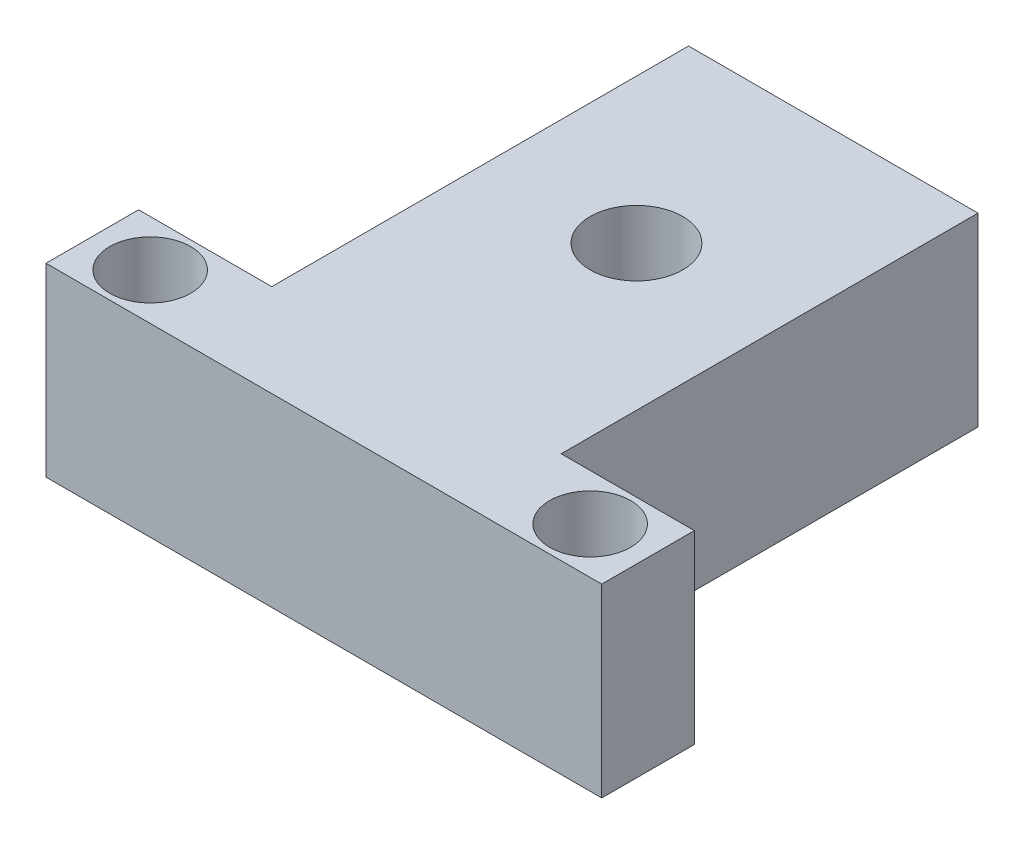
SolidWorks part; units mm, degrees
ref_plane "Front Plane" through (0, 0, 0) normal (0, 0, 1) x (1, 0, 0)
ref_plane "Top Plane" through (0, 0, 0) normal (0, 1, 0) x (1, 0, 0)
ref_plane "Right Plane" through (0, 0, 0) normal (1, 0, 0) x (0, 0, -1)
sketch "Sketch1" plane through (0, 0, 0) normal (0, 1, 0) x (1, 0, 0)
  line L1 (0, 0) -> (48, 0)
  line L2 (0, 0) -> (0, 8)
  line L3 (11.5, 44) -> (36.5, 44)
  line L4 (48, 0) -> (48, 8)
  line L6 (11.5, 44) -> (11.5, 8)
  line L9 (0, 8) -> (11.5, 8)
  line L13 (48, 8) -> (36.5, 8)
  line L14 (36.5, 44) -> (36.5, 8)
  circle A0 centre (5, 4) radius 3.5
  circle A1 centre (43, 4) radius 3.5
  circle A2 centre (24, 27) radius 4
  dimension "D6" = 11.5
  dimension "D2" = 48
extrude "Boss-Extrude1" add sketch "Sketch1" along normal blind 16
